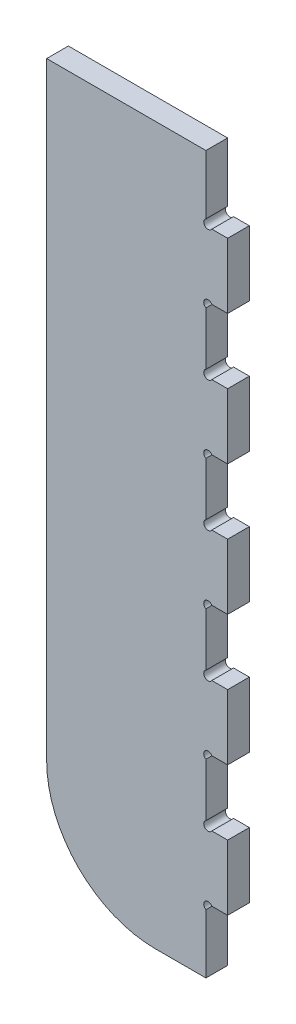
SolidWorks part; units mm, degrees
ref_plane "Front Plane" through (0, 0, 0) normal (0, 0, 1) x (1, 0, 0)
ref_plane "Top Plane" through (0, 0, 0) normal (0, 1, 0) x (1, 0, 0)
ref_plane "Right Plane" through (0, 0, 0) normal (1, 0, 0) x (0, 0, -1)
sketch "Sketch1" plane through (0, 0, 0) normal (0, 0, 1) x (1, 0, 0)
  line L0 (-63.4615, 75.4121) -> (36.5385, 75.4121) construction
  line L1 (36.5385, -42.1879) -> (27.8036, -42.1879)
  line L2 (-63.4615, -18.1879) -> (-63.4615, 317.8121)
  line L3 (-3.4615, -78.1879) -> (24.5385, -78.1879)
  line L4 (32.9271, -6.1879) -> (32.9271, -42.1879) construction
  line L5 (24.5385, 75.4121) -> (24.5385, 98.5109)
  line L6 (32.9271, -42.1879) -> (32.9271, -24.1879) construction
  line L7 (36.5385, -6.1879) -> (27.8036, -6.1879)
  line L8 (24.5385, -2.8867) -> (24.5385, 26.5109)
  line L9 (27.8036, 29.8121) -> (36.5385, 29.8121)
  line L10 (36.5385, -6.1879) -> (36.5385, -42.1879)
  line L11 (36.5385, 65.8121) -> (27.8036, 65.8121)
  line L12 (24.5385, 69.1133) -> (24.5385, 75.4121)
  line L13 (32.9271, -24.1879) -> (17.807, -24.1879) construction
  line L14 (36.5385, 65.8121) -> (36.5385, 29.8121)
  line L15 (25.7385, -42.1879) -> (25.7385, -43.78) construction
  line L16 (24.5385, -42.1879) -> (24.5385, -44.6334) construction
  line L17 (24.5385, -44.6334) -> (24.5385, -43.4107) construction
  line L18 (24.5385, -43.4107) -> (26.1301, -43.4107) construction
  line L19 (24.5385, -45.4891) -> (24.5385, -78.1879)
  line L20 (33.7214, 29.8121) -> (33.7214, -6.1879) construction
  line L21 (33.7214, -6.1879) -> (33.7214, 11.8121) construction
  line L22 (33.7214, 11.8121) -> (17.1837, 11.8121) construction
  line L23 (36.5385, 47.8121) -> (17.807, 47.8121) construction
  line L24 (-63.4615, 317.8121) -> (24.5385, 317.8121)
  line L25 (10.5385, -78.1879) -> (10.5385, 317.8121) construction
  line L26 (10.5385, 317.8121) -> (10.5385, 119.8121) construction
  line L27 (10.5385, 119.8121) -> (-91.8314, 119.8121) construction
  line L28 (27.8036, 101.8121) -> (36.5385, 101.8121)
  line L29 (36.5385, 119.8121) -> (36.5385, 137.8121)
  line L30 (36.5385, 137.8121) -> (27.8036, 137.8121)
  line L32 (33.7214, 101.8121) -> (33.7214, 65.8121) construction
  line L33 (33.7214, 65.8121) -> (33.7214, 83.8121) construction
  line L34 (33.7214, 83.8121) -> (12.5243, 83.8121) construction
  line L35 (10.5385, 119.8121) -> (74.8598, 119.8121) construction
  line L36 (36.5385, 119.8121) -> (36.5385, 101.8121)
  line L38 (36.5385, 281.8121) -> (27.8036, 281.8121)
  line L39 (36.5385, 245.8121) -> (36.5385, 281.8121)
  line L40 (36.5385, 245.8121) -> (27.8036, 245.8121)
  line L42 (27.8036, 209.8121) -> (36.5385, 209.8121)
  line L43 (36.5385, 173.8121) -> (36.5385, 209.8121)
  line L44 (36.5385, 173.8121) -> (27.8036, 173.8121)
  line L45 (24.5385, 170.5109) -> (24.5385, 164.2121)
  line L46 (24.5385, 164.2121) -> (24.5385, 141.1133)
  line L47 (24.5385, 285.1133) -> (24.5385, 317.8121)
  line L49 (24.5385, 213.1133) -> (24.5385, 242.5109)
  arc A0 (-63.4615, -18.1879) -> (-3.4615, -78.1879) centre (-3.4615, -18.1879) ccw
  circle A1 centre (24.5385, -42.1879) radius 2.4 construction
  arc A2 (27.8036, -42.1879) -> (24.5385, -45.4891) centre (25.7385, -43.4107) ccw
  arc A3 (27.8036, -6.1879) -> (24.5385, -2.8867) centre (25.7385, -4.9652) cw
  arc A4 (27.8036, 29.8121) -> (24.5385, 26.5109) centre (25.7385, 28.5893) ccw
  arc A5 (27.8036, 65.8121) -> (24.5385, 69.1133) centre (25.7385, 67.0348) cw
  arc A6 (27.8036, 101.8121) -> (24.5385, 98.5109) centre (25.7385, 100.5893) ccw
  arc A7 (27.8036, 281.8121) -> (24.5385, 285.1133) centre (25.7385, 283.0348) cw
  arc A8 (27.8036, 245.8121) -> (24.5385, 242.5109) centre (25.7385, 244.5893) ccw
  arc A9 (27.8036, 209.8121) -> (24.5385, 213.1133) centre (25.7385, 211.0348) cw
  arc A10 (27.8036, 173.8121) -> (24.5385, 170.5109) centre (25.7385, 172.5893) ccw
  arc A11 (27.8036, 137.8121) -> (24.5385, 141.1133) centre (25.7385, 139.0348) cw
  point P6 (-63.4615, -78.1879)
  dimension "D3" = 60
  dimension "D8" = 4.8
  dimension "D9" = 4.8
  dimension "D1" = 36
  dimension "D2" = 12
  dimension "D4" = 36
  dimension "D5" = 36
  dimension "D6" = 36
  dimension "D7" = 36
  dimension "D10" = 396
  dimension "D11" = 36
  dimension "D12" = 36
extrude "Boss-Extrude1" add sketch "Sketch1" along normal blind 12
